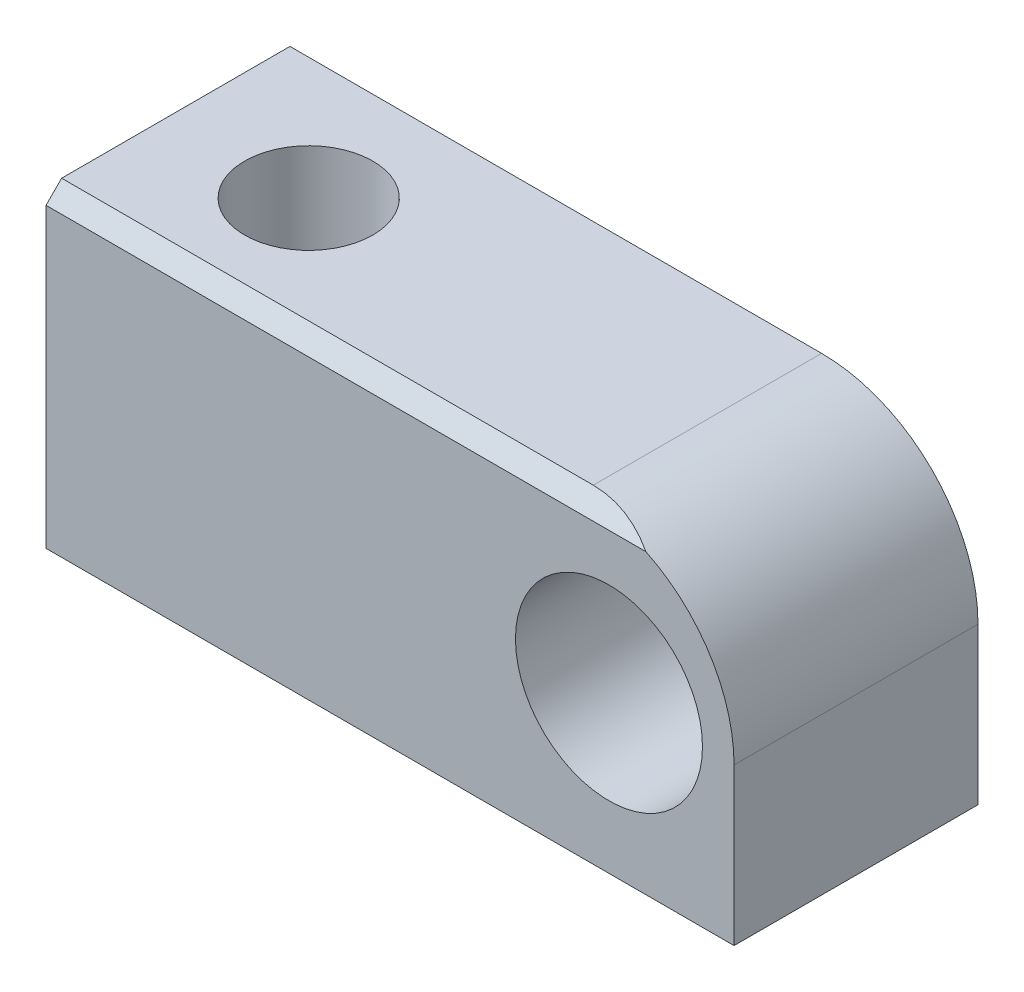
SolidWorks part; units mm, degrees
ref_plane "Plan de face" through (0, 0, 0) normal (0, 0, 1) x (1, 0, 0)
ref_plane "Plan de dessus" through (0, 0, 0) normal (0, 1, 0) x (1, 0, 0)
ref_plane "Plan de droite" through (0, 0, 0) normal (1, 0, 0) x (0, 0, -1)
sketch "Esquisse1" plane through (0, 0, 0) normal (0, 0, 1) x (1, 0, 0)
  line L0 (0, 0) -> (-22, 0)
  line L1 (-22, 0) -> (-22, 10)
  line L2 (-22, 10) -> (-5, 10)
  line L3 (0, 5) -> (0, 0)
  arc A0 (0, 5) -> (-5, 10) centre (-5, 5) ccw
  circle A1 centre (-4, 5) radius 2.99
  dimension "D1" = 5
  dimension "D4" = 4
  dimension "D5" = 5
  dimension "D6" = 5.98
  dimension "D2" = 10
  dimension "D3" = 22
extrude "Extrusion1" add sketch "Esquisse1" along normal mid plane 7.8
sketch "Esquisse2" plane through (0, 0, 0) normal (0, -1, 0) x (1, 0, 0)
  line L0 (-17.5, 0) -> (-22, 0) construction
  line L1 (-22, 3.9) -> (-22, -3.9) construction
  circle A0 centre (-17.5, 0) radius 2.05
  dimension "D2" = 4.1
  dimension "D1" = 4.5
extrude "Enlèv. mat.-Extru.1" cut sketch "Esquisse2" against normal through all
sketch "Esquisse3" plane through (-22, 0, 0) normal (-1, 0, 0) x (0, 0, 1)
  line L0 (3.9, 10) -> (3.9, 9.5)
  line L1 (3.9, 10) -> (3.9, 0) construction
  line L2 (3.9, 9.5) -> (3.4, 10)
  line L3 (3.9, 10) -> (-3.9, 10) construction
  line L4 (3.4, 10) -> (3.9, 10)
  dimension "D1" = 0.5
  dimension "D2" = 45
extrude "Enlèv. mat.-Extru.2" cut sketch "Esquisse3" against normal through all
